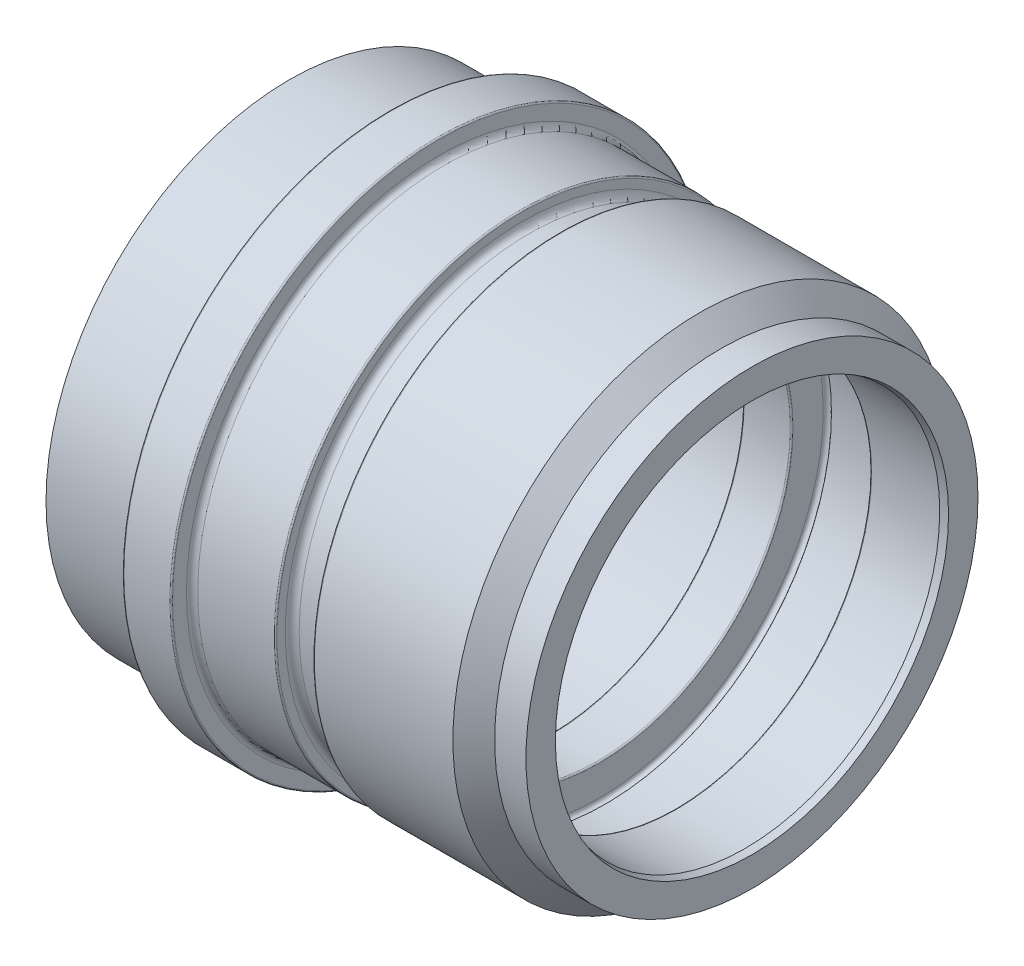
SolidWorks part; units mm, degrees
ref_plane "Front" through (0, 0, 0) normal (0, 0, 1) x (1, 0, 0)
ref_plane "Top" through (0, 0, 0) normal (0, 1, 0) x (1, 0, 0)
ref_plane "Right" through (0, 0, 0) normal (1, 0, 0) x (0, 0, -1)
sketch "Sketch1" plane through (0, 0, 0) normal (0, 0, 1) x (1, 0, 0)
  line L0 (0, 0) -> (-93.4733, 0) construction
  line L1 (0, -13.5831) -> (0, 60.7666) construction
  line L2 (0, 36.3) -> (0, 38.3)
  line L3 (-0.2, 38.5) -> (-6.8, 38.5)
  line L4 (-7, 38.3) -> (-7, 35.2)
  line L5 (-7.2, 35) -> (-21.5, 35)
  line L6 (-21.5, 35) -> (-21.5, 33.0774)
  line L7 (-21.5, 33.0774) -> (-20.5, 32.5)
  line L8 (-20.5, 32.5) -> (-14.8, 32.5)
  line L9 (-14, 31.7) -> (-14, 28)
  line L10 (-14, 28) -> (-9.2, 28)
  line L11 (-9, 28.2) -> (-9, 29.8)
  line L12 (-8.8, 30) -> (15.8, 30)
  line L13 (16, 29.8) -> (16, 27.9)
  line L14 (16.2, 27.7) -> (22.8, 27.7)
  line L15 (23, 27.9) -> (23, 32.25)
  line L16 (23.933, 32.5) -> (33.6, 32.5)
  line L17 (34, 32.1) -> (34, 28.2)
  line L18 (34.2, 28) -> (44, 28)
  line L19 (44, 28) -> (45, 28.2679)
  line L20 (45, 28.2679) -> (45, 32.5)
  line L21 (45, 32.5) -> (40.5, 32.5)
  line L22 (40.5, 32.5) -> (37.5, 35.5)
  line L23 (37.5, 35.5) -> (17.6, 35.5)
  line L24 (17.4, 35.3) -> (17.4, 34.1)
  line L25 (16.4, 33.1) -> (13, 33.1)
  line L26 (12, 34.1) -> (12, 35.3)
  line L27 (11.8, 35.5) -> (0.8, 35.5)
  arc A0 (-14.8, 32.5) -> (-14, 31.7) centre (-14.8, 31.7) cw
  arc A1 (0, 38.3) -> (-0.2, 38.5) centre (-0.2, 38.3) ccw
  arc A2 (-6.8, 38.5) -> (-7, 38.3) centre (-6.8, 38.3) ccw
  arc A3 (0, 36.3) -> (0.8, 35.5) centre (0.8, 36.3) ccw
  arc A4 (-7, 35.2) -> (-7.2, 35) centre (-7.2, 35.2) cw
  arc A5 (17.6, 35.5) -> (17.4, 35.3) centre (17.6, 35.3) ccw
  arc A6 (12, 35.3) -> (11.8, 35.5) centre (11.8, 35.3) ccw
  arc A9 (34, 28.2) -> (34.2, 28) centre (34.2, 28.2) ccw
  arc A10 (22.8, 27.7) -> (23, 27.9) centre (22.8, 27.9) ccw
  arc A11 (33.6, 32.5) -> (34, 32.1) centre (33.6, 32.1) cw
  arc A12 (23, 32.25) -> (23.933, 32.5) centre (23.5, 32.25) cw
  arc A13 (16, 27.9) -> (16.2, 27.7) centre (16.2, 27.9) ccw
  arc A14 (15.8, 30) -> (16, 29.8) centre (15.8, 29.8) cw
  arc A15 (-9, 29.8) -> (-8.8, 30) centre (-8.8, 29.8) cw
  arc A16 (-9.2, 28) -> (-9, 28.2) centre (-9.2, 28.2) ccw
  arc A17 (13, 33.1) -> (12, 34.1) centre (13, 34.1) cw
  arc A18 (17.4, 34.1) -> (16.4, 33.1) centre (16.4, 34.1) cw
  point P35 (0, 38.5)
  point P40 (0, 35.5)
  point P61 (16, 27.7)
  dimension "D29" = 0.8
  dimension "D30" = 0.2
  dimension "D31" = 0.8
  dimension "D32" = 0.2
  dimension "D33" = 0.2
  dimension "D35" = 0.2
  dimension "D36" = 0.4
  dimension "D37" = 0.2
  dimension "D39" = 0.5
  dimension "D40" = 0.25
  dimension "D41" = 1
  dimension "D2" = 66.5
  dimension "D3" = 7
  dimension "D4" = 56
  dimension "D5" = 60
  dimension "D6" = 65
  dimension "D7" = 11
  dimension "D8" = 22
  dimension "D9" = 54
  dimension "D10" = 25
  dimension "D11" = 7.5
  dimension "D12" = 1
  dimension "D13" = 30
  dimension "D14" = 77
  dimension "D15" = 70
  dimension "D16" = 71
  dimension "D17" = 66.2
  dimension "D18" = 5.4
  dimension "D19" = 33
  dimension "D20" = 65
  dimension "D21" = 65
  dimension "D22" = 15
  dimension "D23" = 1
  dimension "D24" = 45
  dimension "D25" = 4.5
  dimension "D26" = 55.4
  dimension "D27" = 7
  dimension "D28" = 45
  dimension "D38" = 56
revolve "Base-Revolve" add sketch "Sketch1" angle 360 about L0
